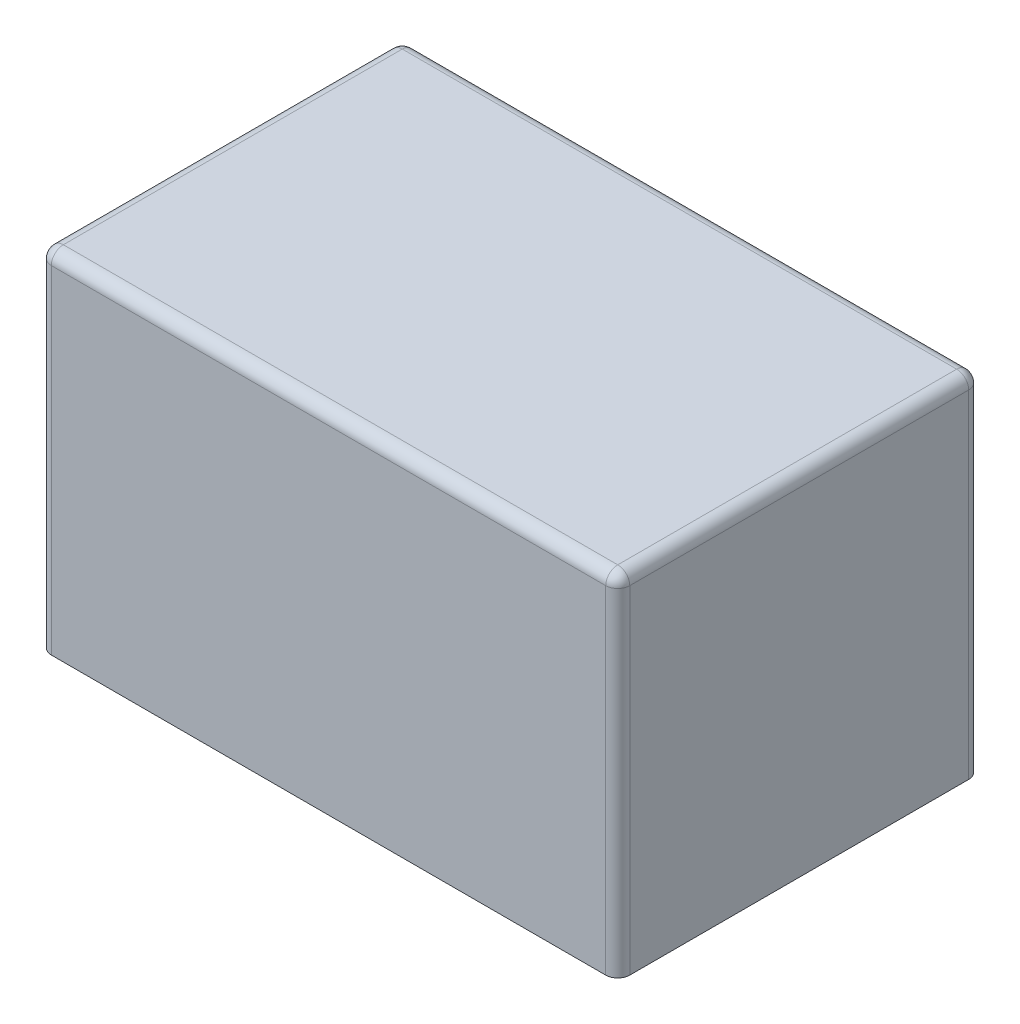
SolidWorks part; units mm, degrees
ref_plane "Front Plane" through (0, 0, 0) normal (0, 0, 1) x (1, 0, 0)
ref_plane "Top Plane" through (0, 0, 0) normal (0, 1, 0) x (1, 0, 0)
ref_plane "Right Plane" through (0, 0, 0) normal (1, 0, 0) x (0, 0, -1)
sketch "Sketch1" plane through (0, 0, 0) normal (0, 1, 0) x (1, 0, 0)
  line L1 (7.65, 4.8) -> (-7.65, 4.8)
  line L2 (7.65, 4.8) -> (7.65, -4.8)
  line L3 (7.65, -4.8) -> (-7.65, -4.8)
  line L4 (-7.65, 4.8) -> (-7.65, -4.8)
  line L5 (7.65, 4.8) -> (-7.65, -4.8) construction
  line L6 (7.65, -4.8) -> (-7.65, 4.8) construction
  point P0 (0, 0)
  dimension "D1" = 15.3
  dimension "D2" = 9.6
extrude "Boss-Extrude1" add sketch "Sketch1" along normal blind 9.24
fillet "Fillet1" radius 0.318 8 edges at (-7.65, 4.62, -4.8) (7.65, 4.62, -4.8) (7.65, 4.62, 4.8) (7.65, 9.24, 0) (0, 9.24, -4.8) (0, 9.24, 4.8) (-7.65, 9.24, 0) (-7.65, 4.62, 4.8)
